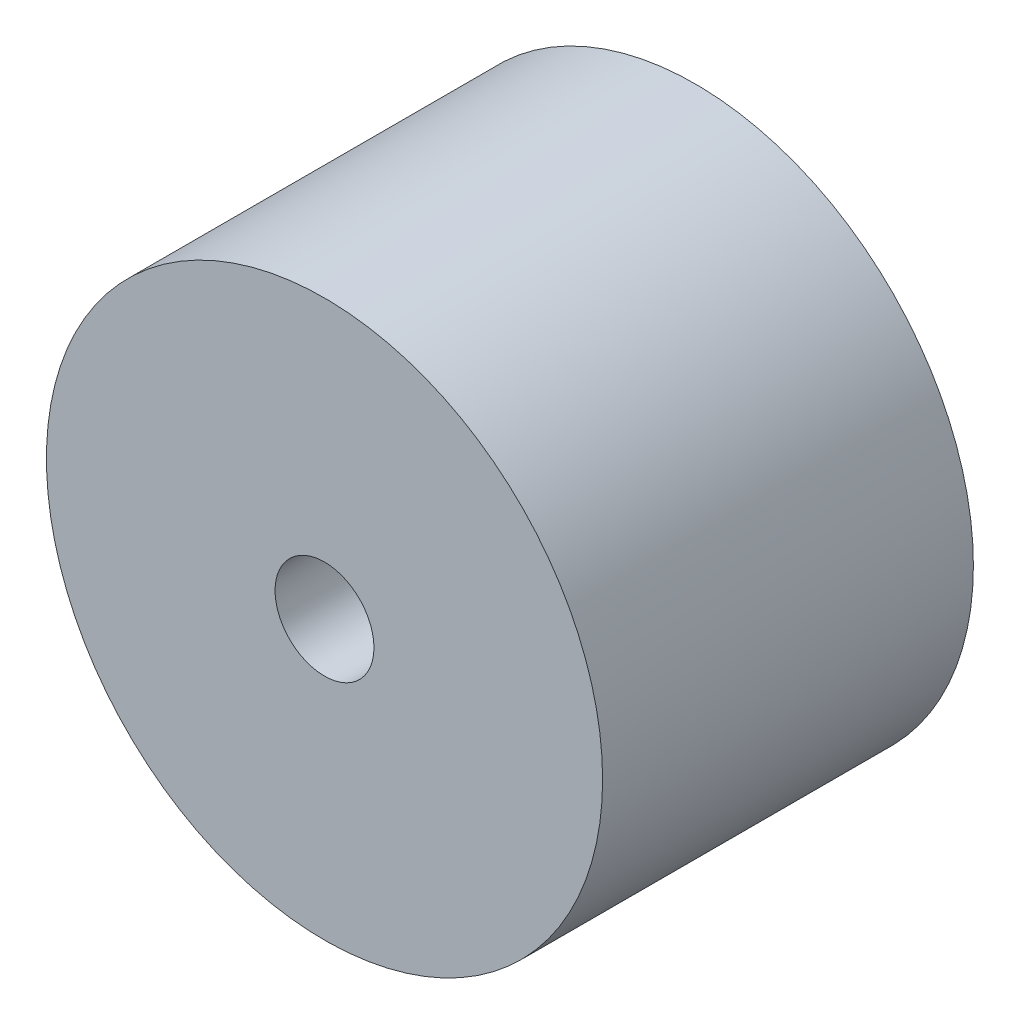
SolidWorks part; units mm, degrees
ref_plane "Front Plane" through (0, 0, 0) normal (0, 0, 1) x (1, 0, 0)
ref_plane "Top Plane" through (0, 0, 0) normal (0, 1, 0) x (1, 0, 0)
ref_plane "Right Plane" through (0, 0, 0) normal (1, 0, 0) x (0, 0, -1)
sketch "Sketch1" plane through (0, 0, 0) normal (0, 0, 1) x (1, 0, 0)
  circle A0 centre (0, 0) radius 2.25
  circle A1 centre (0, 0) radius 0.4
  dimension "D1" = 0.8
  dimension "D2" = 4.5
extrude "Boss-Extrude1" add sketch "Sketch1" along normal blind 3
